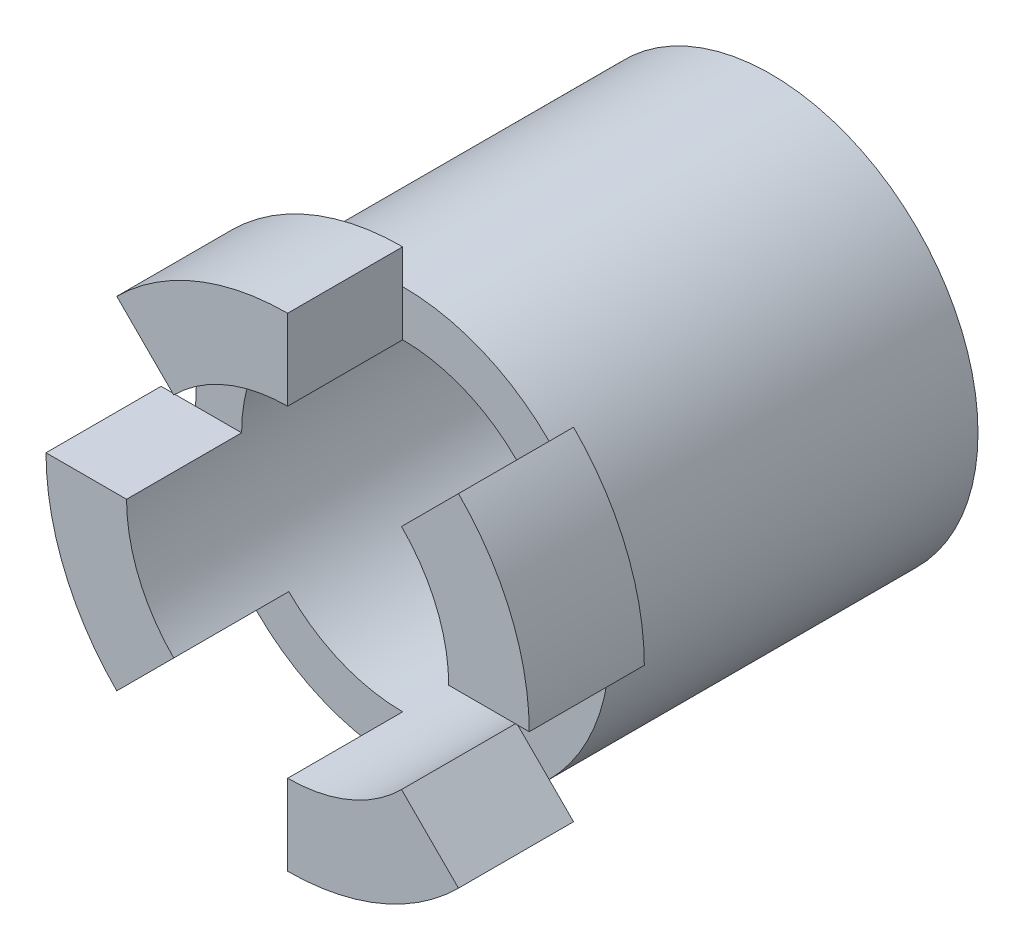
SolidWorks part; units mm, degrees
ref_plane "Front Plane" through (0, 0, 0) normal (0, 0, 1) x (1, 0, 0)
ref_plane "Top Plane" through (0, 0, 0) normal (0, 1, 0) x (1, 0, 0)
ref_plane "Right Plane" through (0, 0, 0) normal (1, 0, 0) x (0, 0, -1)
sketch "Sketch1" plane through (0, 0, 0) normal (0, 0, 1) x (1, 0, 0)
  circle A0 centre (0, 0) radius 4.5
  dimension "D1" = 9
extrude "Boss-Extrude1" add sketch "Sketch1" along normal blind 8
sketch "Sketch2" plane through (0, 0, 8) normal (0, 0, 1) x (1, 0, 0)
  circle A0 centre (0, 0) radius 3.5
  dimension "D1" = 7
extrude "Cut-Extrude1" cut sketch "Sketch2" against normal blind 6.5
sketch "Sketch3" plane through (0, 0, 8) normal (0, 0, 1) x (1, 0, 0)
  line L0 (0, 5.25) -> (0, 3.5)
  line L1 (-5.25, 0) -> (-3.5, 0)
  line L2 (-3.7123, 3.7123) -> (-2.4749, 2.4749)
  line L3 (-3.7123, -3.7123) -> (-2.4749, -2.4749)
  line L4 (2.4749, 2.4749) -> (3.7123, 3.7123)
  line L5 (0, -3.5) -> (0, -5.25)
  line L6 (2.4749, -2.4749) -> (3.7123, -3.7123)
  line L7 (3.5, 0) -> (5.25, 0)
  arc A0 (0, 3.5) -> (-2.4749, 2.4749) centre (0, 0) ccw
  arc A1 (0, 5.25) -> (-3.7123, 3.7123) centre (0, 0) ccw
  arc A2 (3.5, 0) -> (2.4749, 2.4749) centre (0, 0) ccw
  arc A3 (5.25, 0) -> (3.7123, 3.7123) centre (0, 0) ccw
  arc A4 (0, -5.25) -> (3.7123, -3.7123) centre (0, 0) ccw
  arc A5 (0, -3.5) -> (2.4749, -2.4749) centre (0, 0) ccw
  arc A6 (-3.5, 0) -> (-2.4749, -2.4749) centre (0, 0) ccw
  arc A7 (-5.25, 0) -> (-3.7123, -3.7123) centre (0, 0) ccw
  point P1 (0, 0)
  dimension "D1" = 7
  dimension "D2" = 10.5
  dimension "D3" = 45
  dimension "D4" = 45
extrude "Boss-Extrude2" add sketch "Sketch3" along normal blind 2.5
